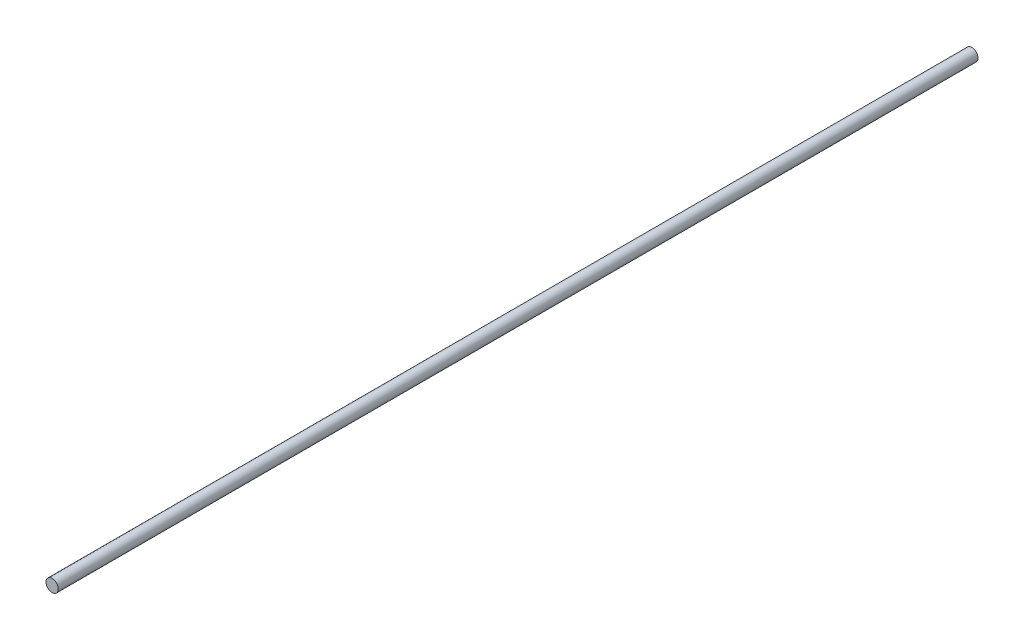
SolidWorks part; units mm, degrees
ref_plane "前视基准面" through (0, 0, 0) normal (0, 0, 1) x (1, 0, 0)
ref_plane "上视基准面" through (0, 0, 0) normal (0, 1, 0) x (1, 0, 0)
ref_plane "右视基准面" through (0, 0, 0) normal (1, 0, 0) x (0, 0, -1)
sketch "草图1" plane through (0, 0, 0) normal (0, 0, 1) x (1, 0, 0)
  circle A0 centre (0, 0) radius 4
  dimension "D1" = 8
extrude "凸台-拉伸1" add sketch "草图1" along normal blind 600
